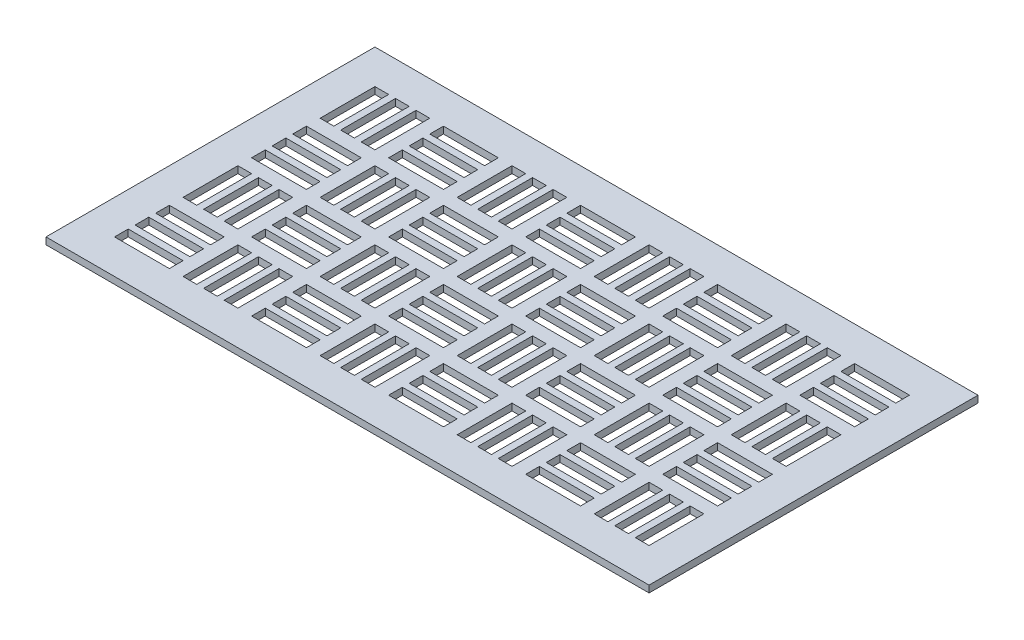
SolidWorks part; units mm, degrees
ref_plane "Front Plane" through (0, 0, 0) normal (0, 0, 1) x (1, 0, 0)
ref_plane "Top Plane" through (0, 0, 0) normal (0, 1, 0) x (1, 0, 0)
ref_plane "Right Plane" through (0, 0, 0) normal (1, 0, 0) x (0, 0, -1)
sketch "Sketch2" plane through (0, 0, 0) normal (0, 1, 0) x (1, 0, 0)
  line L0 (-284.5131, 55.5629) -> (-284.5131, 4.7629)
  line L1 (-328.9631, -217.4871) -> (229.8369, -217.4871)
  line L2 (-328.9631, -217.4871) -> (-328.9631, 87.3129)
  line L3 (-328.9631, 87.3129) -> (229.8369, 87.3129)
  line L4 (229.8369, -217.4871) -> (229.8369, 87.3129)
  line L5 (-316.2631, 74.6129) -> (217.1369, 74.6129)
  line L6 (-316.2631, 74.6129) -> (-316.2631, -204.7871)
  line L7 (-316.2631, -204.7871) -> (217.1369, -204.7871)
  line L8 (217.1369, 74.6129) -> (217.1369, -204.7871)
  line L9 (-297.2131, 55.5629) -> (-284.5131, 55.5629)
  line L10 (-297.2131, 55.5629) -> (-297.2131, 4.7629)
  line L11 (-297.2131, 4.7629) -> (-284.5131, 4.7629)
  line L12 (-246.4131, 55.5629) -> (-246.4131, 4.7629)
  line L13 (-233.7131, 55.5629) -> (-182.9131, 55.5629)
  line L14 (-233.7131, 55.5629) -> (-233.7131, 42.8629)
  line L15 (-233.7131, 4.7629) -> (-182.9131, 4.7629)
  line L16 (-182.9131, 55.5629) -> (-182.9131, 42.8629)
  line L17 (-233.7131, -7.9371) -> (-221.0131, -7.9371)
  line L18 (-233.7131, -7.9371) -> (-233.7131, -58.7371)
  line L19 (-233.7131, -58.7371) -> (-221.0131, -58.7371)
  line L20 (-182.9131, -7.9371) -> (-182.9131, -58.7371)
  line L21 (-246.4131, -7.9371) -> (-297.2131, -7.9371)
  line L22 (-246.4131, -7.9371) -> (-246.4131, -20.6371)
  line L23 (-246.4131, -58.7371) -> (-297.2131, -58.7371)
  line L24 (-297.2131, -7.9371) -> (-297.2131, -20.6371)
  line L25 (-259.1131, 4.7629) -> (-246.4131, 4.7629)
  line L26 (-278.1631, 4.7629) -> (-278.1631, 55.5629)
  line L27 (-278.1631, 55.5629) -> (-265.4631, 55.5629)
  line L28 (-265.4631, 55.5629) -> (-265.4631, 4.7629)
  line L29 (-278.1631, 55.5629) -> (-265.4631, 55.5629)
  line L30 (-259.1131, 4.7629) -> (-259.1131, 55.5629)
  line L31 (-221.0131, -7.9371) -> (-221.0131, -58.7371)
  line L32 (-233.7131, 17.4629) -> (-233.7131, 4.7629)
  line L33 (-214.6631, -58.7371) -> (-214.6631, -7.9371)
  line L34 (-214.6631, -7.9371) -> (-201.9631, -7.9371)
  line L35 (-201.9631, -7.9371) -> (-201.9631, -58.7371)
  line L36 (-182.9131, 17.4629) -> (-182.9131, 4.7629)
  line L37 (-195.6131, -58.7371) -> (-195.6131, -7.9371)
  line L38 (-233.7131, 42.8629) -> (-182.9131, 42.8629)
  line L39 (-278.1631, 4.7629) -> (-265.4631, 4.7629)
  line L40 (-182.9131, 36.5129) -> (-233.7131, 36.5129)
  line L41 (-233.7131, 36.5129) -> (-233.7131, 23.8129)
  line L42 (-233.7131, 23.8129) -> (-182.9131, 23.8129)
  line L43 (-259.1131, 55.5629) -> (-246.4131, 55.5629)
  line L44 (-182.9131, 17.4629) -> (-233.7131, 17.4629)
  line L45 (-297.2131, -20.6371) -> (-246.4131, -20.6371)
  line L46 (-246.4131, -46.0371) -> (-246.4131, -58.7371)
  line L47 (-246.4131, -26.9871) -> (-297.2131, -26.9871)
  line L48 (-297.2131, -26.9871) -> (-297.2131, -39.6871)
  line L49 (-297.2131, -39.6871) -> (-246.4131, -39.6871)
  line L50 (-195.6131, -58.7371) -> (-182.9131, -58.7371)
  line L51 (-246.4131, -46.0371) -> (-297.2131, -46.0371)
  line L52 (-297.2131, -46.0371) -> (-297.2131, -58.7371)
  line L53 (-297.2131, -26.9871) -> (-297.2131, -39.6871)
  line L54 (-246.4131, -26.9871) -> (-246.4131, -39.6871)
  line L55 (-214.6631, -7.9371) -> (-201.9631, -7.9371)
  line L56 (-195.6131, -7.9371) -> (-182.9131, -7.9371)
  line L57 (-214.6631, -58.7371) -> (-201.9631, -58.7371)
  line L58 (-233.7131, 36.5129) -> (-233.7131, 23.8129)
  line L59 (-182.9131, 36.5129) -> (-182.9131, 23.8129)
  line L60 (-170.2131, 55.5629) -> (-170.2131, 4.7629)
  line L61 (-157.5131, 55.5629) -> (-157.5131, 4.7629)
  line L62 (-170.2131, 55.5629) -> (-157.5131, 55.5629)
  line L63 (-170.2131, 4.7629) -> (-157.5131, 4.7629)
  line L64 (-151.1631, 4.7629) -> (-151.1631, 55.5629)
  line L65 (-138.4631, 55.5629) -> (-138.4631, 4.7629)
  line L66 (-132.1131, 4.7629) -> (-132.1131, 55.5629)
  line L67 (-119.4131, 55.5629) -> (-119.4131, 4.7629)
  line L68 (-132.1131, 55.5629) -> (-119.4131, 55.5629)
  line L69 (-151.1631, 55.5629) -> (-138.4631, 55.5629)
  line L70 (-151.1631, 4.7629) -> (-138.4631, 4.7629)
  line L71 (-132.1131, 4.7629) -> (-119.4131, 4.7629)
  line L72 (-106.7131, 4.7629) -> (-55.9131, 4.7629)
  line L73 (-55.9131, 17.4629) -> (-106.7131, 17.4629)
  line L74 (-106.7131, 23.8129) -> (-55.9131, 23.8129)
  line L75 (-55.9131, 36.5129) -> (-106.7131, 36.5129)
  line L76 (-106.7131, 42.8629) -> (-55.9131, 42.8629)
  line L77 (-106.7131, 55.5629) -> (-55.9131, 55.5629)
  line L78 (-55.9131, -7.9371) -> (-55.9131, -58.7371)
  line L79 (-68.6131, -58.7371) -> (-68.6131, -7.9371)
  line L80 (-74.9631, -7.9371) -> (-74.9631, -58.7371)
  line L81 (-87.6631, -58.7371) -> (-87.6631, -7.9371)
  line L82 (-94.0131, -7.9371) -> (-94.0131, -58.7371)
  line L83 (-106.7131, -7.9371) -> (-106.7131, -58.7371)
  line L84 (-119.4131, -58.7371) -> (-170.2131, -58.7371)
  line L85 (-119.4131, -46.0371) -> (-119.4131, -58.7371)
  line L86 (-119.4131, -46.0371) -> (-170.2131, -46.0371)
  line L87 (-170.2131, -39.6871) -> (-119.4131, -39.6871)
  line L88 (-119.4131, -26.9871) -> (-119.4131, -39.6871)
  line L89 (-119.4131, -26.9871) -> (-170.2131, -26.9871)
  line L90 (-170.2131, -20.6371) -> (-119.4131, -20.6371)
  line L91 (-119.4131, -7.9371) -> (-119.4131, -20.6371)
  line L92 (-119.4131, -7.9371) -> (-170.2131, -7.9371)
  line L93 (-170.2131, -7.9371) -> (-170.2131, -20.6371)
  line L94 (-170.2131, -26.9871) -> (-170.2131, -39.6871)
  line L95 (-170.2131, -46.0371) -> (-170.2131, -58.7371)
  line L96 (-106.7131, -58.7371) -> (-94.0131, -58.7371)
  line L97 (-87.6631, -58.7371) -> (-74.9631, -58.7371)
  line L98 (-68.6131, -58.7371) -> (-55.9131, -58.7371)
  line L99 (-68.6131, -7.9371) -> (-55.9131, -7.9371)
  line L100 (-55.9131, 17.4629) -> (-55.9131, 4.7629)
  line L101 (-55.9131, 36.5129) -> (-55.9131, 23.8129)
  line L102 (-55.9131, 55.5629) -> (-55.9131, 42.8629)
  line L103 (-106.7131, 55.5629) -> (-106.7131, 42.8629)
  line L104 (-106.7131, 36.5129) -> (-106.7131, 23.8129)
  line L105 (-106.7131, 17.4629) -> (-106.7131, 4.7629)
  line L106 (-106.7131, -7.9371) -> (-94.0131, -7.9371)
  line L107 (-87.6631, -7.9371) -> (-74.9631, -7.9371)
  line L108 (-43.2131, 55.5629) -> (-43.2131, 4.7629)
  line L109 (-30.5131, 55.5629) -> (-30.5131, 4.7629)
  line L110 (-43.2131, 55.5629) -> (-30.5131, 55.5629)
  line L111 (-43.2131, 4.7629) -> (-30.5131, 4.7629)
  line L112 (-24.1631, 4.7629) -> (-24.1631, 55.5629)
  line L113 (-11.4631, 55.5629) -> (-11.4631, 4.7629)
  line L114 (-5.1131, 4.7629) -> (-5.1131, 55.5629)
  line L115 (7.5869, 55.5629) -> (7.5869, 4.7629)
  line L116 (-5.1131, 55.5629) -> (7.5869, 55.5629)
  line L117 (-24.1631, 55.5629) -> (-11.4631, 55.5629)
  line L118 (-24.1631, 4.7629) -> (-11.4631, 4.7629)
  line L119 (-5.1131, 4.7629) -> (7.5869, 4.7629)
  line L120 (20.2869, 4.7629) -> (71.0869, 4.7629)
  line L121 (71.0869, 17.4629) -> (20.2869, 17.4629)
  line L122 (20.2869, 23.8129) -> (71.0869, 23.8129)
  line L123 (71.0869, 36.5129) -> (20.2869, 36.5129)
  line L124 (20.2869, 42.8629) -> (71.0869, 42.8629)
  line L125 (20.2869, 55.5629) -> (71.0869, 55.5629)
  line L126 (71.0869, -7.9371) -> (71.0869, -58.7371)
  line L127 (58.3869, -58.7371) -> (58.3869, -7.9371)
  line L128 (52.0369, -7.9371) -> (52.0369, -58.7371)
  line L129 (39.3369, -58.7371) -> (39.3369, -7.9371)
  line L130 (32.9869, -7.9371) -> (32.9869, -58.7371)
  line L131 (20.2869, -7.9371) -> (20.2869, -58.7371)
  line L132 (7.5869, -58.7371) -> (-43.2131, -58.7371)
  line L133 (7.5869, -46.0371) -> (7.5869, -58.7371)
  line L134 (7.5869, -46.0371) -> (-43.2131, -46.0371)
  line L135 (-43.2131, -39.6871) -> (7.5869, -39.6871)
  line L136 (7.5869, -26.9871) -> (7.5869, -39.6871)
  line L137 (7.5869, -26.9871) -> (-43.2131, -26.9871)
  line L138 (-43.2131, -20.6371) -> (7.5869, -20.6371)
  line L139 (7.5869, -7.9371) -> (7.5869, -20.6371)
  line L140 (7.5869, -7.9371) -> (-43.2131, -7.9371)
  line L141 (-43.2131, -7.9371) -> (-43.2131, -20.6371)
  line L142 (-43.2131, -26.9871) -> (-43.2131, -39.6871)
  line L143 (-43.2131, -46.0371) -> (-43.2131, -58.7371)
  line L144 (20.2869, -58.7371) -> (32.9869, -58.7371)
  line L145 (39.3369, -58.7371) -> (52.0369, -58.7371)
  line L146 (58.3869, -58.7371) -> (71.0869, -58.7371)
  line L147 (58.3869, -7.9371) -> (71.0869, -7.9371)
  line L148 (71.0869, 17.4629) -> (71.0869, 4.7629)
  line L149 (71.0869, 36.5129) -> (71.0869, 23.8129)
  line L150 (71.0869, 55.5629) -> (71.0869, 42.8629)
  line L151 (20.2869, 55.5629) -> (20.2869, 42.8629)
  line L152 (20.2869, 36.5129) -> (20.2869, 23.8129)
  line L153 (20.2869, 17.4629) -> (20.2869, 4.7629)
  line L154 (20.2869, -7.9371) -> (32.9869, -7.9371)
  line L155 (39.3369, -7.9371) -> (52.0369, -7.9371)
  line L156 (83.7869, 55.5629) -> (83.7869, 4.7629)
  line L157 (96.4869, 55.5629) -> (96.4869, 4.7629)
  line L158 (83.7869, 55.5629) -> (96.4869, 55.5629)
  line L159 (83.7869, 4.7629) -> (96.4869, 4.7629)
  line L160 (102.8369, 4.7629) -> (102.8369, 55.5629)
  line L161 (115.5369, 55.5629) -> (115.5369, 4.7629)
  line L162 (121.8869, 4.7629) -> (121.8869, 55.5629)
  line L163 (134.5869, 55.5629) -> (134.5869, 4.7629)
  line L164 (121.8869, 55.5629) -> (134.5869, 55.5629)
  line L165 (102.8369, 55.5629) -> (115.5369, 55.5629)
  line L166 (102.8369, 4.7629) -> (115.5369, 4.7629)
  line L167 (121.8869, 4.7629) -> (134.5869, 4.7629)
  line L168 (147.2869, 4.7629) -> (198.0869, 4.7629)
  line L169 (198.0869, 17.4629) -> (147.2869, 17.4629)
  line L170 (147.2869, 23.8129) -> (198.0869, 23.8129)
  line L171 (198.0869, 36.5129) -> (147.2869, 36.5129)
  line L172 (147.2869, 42.8629) -> (198.0869, 42.8629)
  line L173 (147.2869, 55.5629) -> (198.0869, 55.5629)
  line L174 (198.0869, -7.9371) -> (198.0869, -58.7371)
  line L175 (185.3869, -58.7371) -> (185.3869, -7.9371)
  line L176 (179.0369, -7.9371) -> (179.0369, -58.7371)
  line L177 (166.3369, -58.7371) -> (166.3369, -7.9371)
  line L178 (159.9869, -7.9371) -> (159.9869, -58.7371)
  line L179 (147.2869, -7.9371) -> (147.2869, -58.7371)
  line L180 (134.5869, -58.7371) -> (83.7869, -58.7371)
  line L181 (134.5869, -46.0371) -> (134.5869, -58.7371)
  line L182 (134.5869, -46.0371) -> (83.7869, -46.0371)
  line L183 (83.7869, -39.6871) -> (134.5869, -39.6871)
  line L184 (134.5869, -26.9871) -> (134.5869, -39.6871)
  line L185 (134.5869, -26.9871) -> (83.7869, -26.9871)
  line L186 (83.7869, -20.6371) -> (134.5869, -20.6371)
  line L187 (134.5869, -7.9371) -> (134.5869, -20.6371)
  line L188 (134.5869, -7.9371) -> (83.7869, -7.9371)
  line L189 (83.7869, -7.9371) -> (83.7869, -20.6371)
  line L190 (83.7869, -26.9871) -> (83.7869, -39.6871)
  line L191 (83.7869, -46.0371) -> (83.7869, -58.7371)
  line L192 (147.2869, -58.7371) -> (159.9869, -58.7371)
  line L193 (166.3369, -58.7371) -> (179.0369, -58.7371)
  line L194 (185.3869, -58.7371) -> (198.0869, -58.7371)
  line L195 (185.3869, -7.9371) -> (198.0869, -7.9371)
  line L196 (198.0869, 17.4629) -> (198.0869, 4.7629)
  line L197 (198.0869, 36.5129) -> (198.0869, 23.8129)
  line L198 (198.0869, 55.5629) -> (198.0869, 42.8629)
  line L199 (147.2869, 55.5629) -> (147.2869, 42.8629)
  line L200 (147.2869, 36.5129) -> (147.2869, 23.8129)
  line L201 (147.2869, 17.4629) -> (147.2869, 4.7629)
  line L202 (147.2869, -7.9371) -> (159.9869, -7.9371)
  line L203 (166.3369, -7.9371) -> (179.0369, -7.9371)
  line L204 (-170.2131, -71.4371) -> (-170.2131, -122.2371)
  line L205 (-157.5131, -71.4371) -> (-157.5131, -122.2371)
  line L206 (-170.2131, -71.4371) -> (-157.5131, -71.4371)
  line L207 (-170.2131, -122.2371) -> (-157.5131, -122.2371)
  line L208 (-151.1631, -122.2371) -> (-151.1631, -71.4371)
  line L209 (-138.4631, -71.4371) -> (-138.4631, -122.2371)
  line L210 (-132.1131, -122.2371) -> (-132.1131, -71.4371)
  line L211 (-119.4131, -71.4371) -> (-119.4131, -122.2371)
  line L212 (-132.1131, -71.4371) -> (-119.4131, -71.4371)
  line L213 (-151.1631, -71.4371) -> (-138.4631, -71.4371)
  line L214 (-151.1631, -122.2371) -> (-138.4631, -122.2371)
  line L215 (-132.1131, -122.2371) -> (-119.4131, -122.2371)
  line L216 (-106.7131, -122.2371) -> (-55.9131, -122.2371)
  line L217 (-55.9131, -109.5371) -> (-106.7131, -109.5371)
  line L218 (-106.7131, -103.1871) -> (-55.9131, -103.1871)
  line L219 (-55.9131, -90.4871) -> (-106.7131, -90.4871)
  line L220 (-106.7131, -84.1371) -> (-55.9131, -84.1371)
  line L221 (-106.7131, -71.4371) -> (-55.9131, -71.4371)
  line L222 (-55.9131, -134.9371) -> (-55.9131, -185.7371)
  line L223 (-68.6131, -185.7371) -> (-68.6131, -134.9371)
  line L224 (-74.9631, -134.9371) -> (-74.9631, -185.7371)
  line L225 (-87.6631, -185.7371) -> (-87.6631, -134.9371)
  line L226 (-94.0131, -134.9371) -> (-94.0131, -185.7371)
  line L227 (-106.7131, -134.9371) -> (-106.7131, -185.7371)
  line L228 (-119.4131, -185.7371) -> (-170.2131, -185.7371)
  line L229 (-119.4131, -173.0371) -> (-119.4131, -185.7371)
  line L230 (-119.4131, -173.0371) -> (-170.2131, -173.0371)
  line L231 (-170.2131, -166.6871) -> (-119.4131, -166.6871)
  line L232 (-119.4131, -153.9871) -> (-119.4131, -166.6871)
  line L233 (-119.4131, -153.9871) -> (-170.2131, -153.9871)
  line L234 (-170.2131, -147.6371) -> (-119.4131, -147.6371)
  line L235 (-119.4131, -134.9371) -> (-119.4131, -147.6371)
  line L236 (-119.4131, -134.9371) -> (-170.2131, -134.9371)
  line L237 (-170.2131, -134.9371) -> (-170.2131, -147.6371)
  line L238 (-170.2131, -153.9871) -> (-170.2131, -166.6871)
  line L239 (-170.2131, -173.0371) -> (-170.2131, -185.7371)
  line L240 (-106.7131, -185.7371) -> (-94.0131, -185.7371)
  line L241 (-87.6631, -185.7371) -> (-74.9631, -185.7371)
  line L242 (-68.6131, -185.7371) -> (-55.9131, -185.7371)
  line L243 (-68.6131, -134.9371) -> (-55.9131, -134.9371)
  line L244 (-55.9131, -109.5371) -> (-55.9131, -122.2371)
  line L245 (-55.9131, -90.4871) -> (-55.9131, -103.1871)
  line L246 (-55.9131, -71.4371) -> (-55.9131, -84.1371)
  line L247 (-106.7131, -71.4371) -> (-106.7131, -84.1371)
  line L248 (-106.7131, -90.4871) -> (-106.7131, -103.1871)
  line L249 (-106.7131, -109.5371) -> (-106.7131, -122.2371)
  line L250 (-106.7131, -134.9371) -> (-94.0131, -134.9371)
  line L251 (-87.6631, -134.9371) -> (-74.9631, -134.9371)
  line L252 (-43.2131, -71.4371) -> (-43.2131, -122.2371)
  line L253 (-30.5131, -71.4371) -> (-30.5131, -122.2371)
  line L254 (-43.2131, -71.4371) -> (-30.5131, -71.4371)
  line L255 (-43.2131, -122.2371) -> (-30.5131, -122.2371)
  line L256 (-24.1631, -122.2371) -> (-24.1631, -71.4371)
  line L257 (-11.4631, -71.4371) -> (-11.4631, -122.2371)
  line L258 (-5.1131, -122.2371) -> (-5.1131, -71.4371)
  line L259 (7.5869, -71.4371) -> (7.5869, -122.2371)
  line L260 (-5.1131, -71.4371) -> (7.5869, -71.4371)
  line L261 (-24.1631, -71.4371) -> (-11.4631, -71.4371)
  line L262 (-24.1631, -122.2371) -> (-11.4631, -122.2371)
  line L263 (-5.1131, -122.2371) -> (7.5869, -122.2371)
  line L264 (20.2869, -122.2371) -> (71.0869, -122.2371)
  line L265 (71.0869, -109.5371) -> (20.2869, -109.5371)
  line L266 (20.2869, -103.1871) -> (71.0869, -103.1871)
  line L267 (71.0869, -90.4871) -> (20.2869, -90.4871)
  line L268 (20.2869, -84.1371) -> (71.0869, -84.1371)
  line L269 (20.2869, -71.4371) -> (71.0869, -71.4371)
  line L270 (71.0869, -134.9371) -> (71.0869, -185.7371)
  line L271 (58.3869, -185.7371) -> (58.3869, -134.9371)
  line L272 (52.0369, -134.9371) -> (52.0369, -185.7371)
  line L273 (39.3369, -185.7371) -> (39.3369, -134.9371)
  line L274 (32.9869, -134.9371) -> (32.9869, -185.7371)
  line L275 (20.2869, -134.9371) -> (20.2869, -185.7371)
  line L276 (7.5869, -185.7371) -> (-43.2131, -185.7371)
  line L277 (7.5869, -173.0371) -> (7.5869, -185.7371)
  line L278 (7.5869, -173.0371) -> (-43.2131, -173.0371)
  line L279 (-43.2131, -166.6871) -> (7.5869, -166.6871)
  line L280 (7.5869, -153.9871) -> (7.5869, -166.6871)
  line L281 (7.5869, -153.9871) -> (-43.2131, -153.9871)
  line L282 (-43.2131, -147.6371) -> (7.5869, -147.6371)
  line L283 (7.5869, -134.9371) -> (7.5869, -147.6371)
  line L284 (7.5869, -134.9371) -> (-43.2131, -134.9371)
  line L285 (-43.2131, -134.9371) -> (-43.2131, -147.6371)
  line L286 (-43.2131, -153.9871) -> (-43.2131, -166.6871)
  line L287 (-43.2131, -173.0371) -> (-43.2131, -185.7371)
  line L288 (20.2869, -185.7371) -> (32.9869, -185.7371)
  line L289 (39.3369, -185.7371) -> (52.0369, -185.7371)
  line L290 (58.3869, -185.7371) -> (71.0869, -185.7371)
  line L291 (58.3869, -134.9371) -> (71.0869, -134.9371)
  line L292 (71.0869, -109.5371) -> (71.0869, -122.2371)
  line L293 (71.0869, -90.4871) -> (71.0869, -103.1871)
  line L294 (71.0869, -71.4371) -> (71.0869, -84.1371)
  line L295 (20.2869, -71.4371) -> (20.2869, -84.1371)
  line L296 (20.2869, -90.4871) -> (20.2869, -103.1871)
  line L297 (20.2869, -109.5371) -> (20.2869, -122.2371)
  line L298 (20.2869, -134.9371) -> (32.9869, -134.9371)
  line L299 (39.3369, -134.9371) -> (52.0369, -134.9371)
  line L300 (83.7869, -71.4371) -> (83.7869, -122.2371)
  line L301 (96.4869, -71.4371) -> (96.4869, -122.2371)
  line L302 (83.7869, -71.4371) -> (96.4869, -71.4371)
  line L303 (83.7869, -122.2371) -> (96.4869, -122.2371)
  line L304 (102.8369, -122.2371) -> (102.8369, -71.4371)
  line L305 (115.5369, -71.4371) -> (115.5369, -122.2371)
  line L306 (121.8869, -122.2371) -> (121.8869, -71.4371)
  line L307 (134.5869, -71.4371) -> (134.5869, -122.2371)
  line L308 (121.8869, -71.4371) -> (134.5869, -71.4371)
  line L309 (102.8369, -71.4371) -> (115.5369, -71.4371)
  line L310 (102.8369, -122.2371) -> (115.5369, -122.2371)
  line L311 (121.8869, -122.2371) -> (134.5869, -122.2371)
  line L312 (147.2869, -122.2371) -> (198.0869, -122.2371)
  line L313 (198.0869, -109.5371) -> (147.2869, -109.5371)
  line L314 (147.2869, -103.1871) -> (198.0869, -103.1871)
  line L315 (198.0869, -90.4871) -> (147.2869, -90.4871)
  line L316 (147.2869, -84.1371) -> (198.0869, -84.1371)
  line L317 (147.2869, -71.4371) -> (198.0869, -71.4371)
  line L318 (198.0869, -134.9371) -> (198.0869, -185.7371)
  line L319 (185.3869, -185.7371) -> (185.3869, -134.9371)
  line L320 (179.0369, -134.9371) -> (179.0369, -185.7371)
  line L321 (166.3369, -185.7371) -> (166.3369, -134.9371)
  line L322 (159.9869, -134.9371) -> (159.9869, -185.7371)
  line L323 (147.2869, -134.9371) -> (147.2869, -185.7371)
  line L324 (134.5869, -185.7371) -> (83.7869, -185.7371)
  line L325 (134.5869, -173.0371) -> (134.5869, -185.7371)
  line L326 (134.5869, -173.0371) -> (83.7869, -173.0371)
  line L327 (83.7869, -166.6871) -> (134.5869, -166.6871)
  line L328 (134.5869, -153.9871) -> (134.5869, -166.6871)
  line L329 (134.5869, -153.9871) -> (83.7869, -153.9871)
  line L330 (83.7869, -147.6371) -> (134.5869, -147.6371)
  line L331 (134.5869, -134.9371) -> (134.5869, -147.6371)
  line L332 (134.5869, -134.9371) -> (83.7869, -134.9371)
  line L333 (83.7869, -134.9371) -> (83.7869, -147.6371)
  line L334 (83.7869, -153.9871) -> (83.7869, -166.6871)
  line L335 (83.7869, -173.0371) -> (83.7869, -185.7371)
  line L336 (147.2869, -185.7371) -> (159.9869, -185.7371)
  line L337 (166.3369, -185.7371) -> (179.0369, -185.7371)
  line L338 (185.3869, -185.7371) -> (198.0869, -185.7371)
  line L339 (185.3869, -134.9371) -> (198.0869, -134.9371)
  line L340 (198.0869, -109.5371) -> (198.0869, -122.2371)
  line L341 (198.0869, -90.4871) -> (198.0869, -103.1871)
  line L342 (198.0869, -71.4371) -> (198.0869, -84.1371)
  line L343 (147.2869, -71.4371) -> (147.2869, -84.1371)
  line L344 (147.2869, -90.4871) -> (147.2869, -103.1871)
  line L345 (147.2869, -109.5371) -> (147.2869, -122.2371)
  line L346 (147.2869, -134.9371) -> (159.9869, -134.9371)
  line L347 (166.3369, -134.9371) -> (179.0369, -134.9371)
  line L348 (-297.2131, -71.4371) -> (-297.2131, -122.2371)
  line L349 (-284.5131, -71.4371) -> (-284.5131, -122.2371)
  line L350 (-297.2131, -71.4371) -> (-284.5131, -71.4371)
  line L351 (-297.2131, -122.2371) -> (-284.5131, -122.2371)
  line L352 (-278.1631, -122.2371) -> (-278.1631, -71.4371)
  line L353 (-265.4631, -71.4371) -> (-265.4631, -122.2371)
  line L354 (-259.1131, -122.2371) -> (-259.1131, -71.4371)
  line L355 (-246.4131, -71.4371) -> (-246.4131, -122.2371)
  line L356 (-259.1131, -71.4371) -> (-246.4131, -71.4371)
  line L357 (-278.1631, -71.4371) -> (-265.4631, -71.4371)
  line L358 (-278.1631, -122.2371) -> (-265.4631, -122.2371)
  line L359 (-259.1131, -122.2371) -> (-246.4131, -122.2371)
  line L360 (-233.7131, -122.2371) -> (-182.9131, -122.2371)
  line L361 (-182.9131, -109.5371) -> (-233.7131, -109.5371)
  line L362 (-233.7131, -103.1871) -> (-182.9131, -103.1871)
  line L363 (-182.9131, -90.4871) -> (-233.7131, -90.4871)
  line L364 (-233.7131, -84.1371) -> (-182.9131, -84.1371)
  line L365 (-233.7131, -71.4371) -> (-182.9131, -71.4371)
  line L366 (-182.9131, -134.9371) -> (-182.9131, -185.7371)
  line L367 (-195.6131, -185.7371) -> (-195.6131, -134.9371)
  line L368 (-201.9631, -134.9371) -> (-201.9631, -185.7371)
  line L369 (-214.6631, -185.7371) -> (-214.6631, -134.9371)
  line L370 (-221.0131, -134.9371) -> (-221.0131, -185.7371)
  line L371 (-233.7131, -134.9371) -> (-233.7131, -185.7371)
  line L372 (-246.4131, -185.7371) -> (-297.2131, -185.7371)
  line L373 (-246.4131, -173.0371) -> (-246.4131, -185.7371)
  line L374 (-246.4131, -173.0371) -> (-297.2131, -173.0371)
  line L375 (-297.2131, -166.6871) -> (-246.4131, -166.6871)
  line L376 (-246.4131, -153.9871) -> (-246.4131, -166.6871)
  line L377 (-246.4131, -153.9871) -> (-297.2131, -153.9871)
  line L378 (-297.2131, -147.6371) -> (-246.4131, -147.6371)
  line L379 (-246.4131, -134.9371) -> (-246.4131, -147.6371)
  line L380 (-246.4131, -134.9371) -> (-297.2131, -134.9371)
  line L381 (-297.2131, -134.9371) -> (-297.2131, -147.6371)
  line L382 (-297.2131, -153.9871) -> (-297.2131, -166.6871)
  line L383 (-297.2131, -173.0371) -> (-297.2131, -185.7371)
  line L384 (-233.7131, -185.7371) -> (-221.0131, -185.7371)
  line L385 (-214.6631, -185.7371) -> (-201.9631, -185.7371)
  line L386 (-195.6131, -185.7371) -> (-182.9131, -185.7371)
  line L387 (-195.6131, -134.9371) -> (-182.9131, -134.9371)
  line L388 (-182.9131, -109.5371) -> (-182.9131, -122.2371)
  line L389 (-182.9131, -90.4871) -> (-182.9131, -103.1871)
  line L390 (-182.9131, -71.4371) -> (-182.9131, -84.1371)
  line L391 (-233.7131, -71.4371) -> (-233.7131, -84.1371)
  line L392 (-233.7131, -90.4871) -> (-233.7131, -103.1871)
  line L393 (-233.7131, -109.5371) -> (-233.7131, -122.2371)
  line L394 (-233.7131, -134.9371) -> (-221.0131, -134.9371)
  line L395 (-214.6631, -134.9371) -> (-201.9631, -134.9371)
  point P56 (-265.4631, 30.1629)
  dimension "D1" = 558.8
  dimension "D2" = 304.8
  dimension "D3" = 12.7
  dimension "D4" = 12.7
  dimension "D5" = 12.7
  dimension "D6" = 12.7
  dimension "D7" = 50.8
  dimension "D8" = 50.8
  dimension "D9" = 19.05
  dimension "D10" = 19.05
  dimension "D11" = 12.7
  dimension "D12" = 12.7
  dimension "D13" = 12.7
  dimension "D14" = 12.7
  dimension "D15" = 50.8
  dimension "D16" = 50.8
  dimension "D17" = 50.8
  dimension "D18" = 50.8
  dimension "D19" = 50.8
  dimension "D20" = 50.8
  dimension "D21" = 19.05
  dimension "D22" = 19.05
  dimension "D23" = 12.7
  dimension "D24" = 6.35
  dimension "D25" = 12.7
  dimension "D26" = 6.35
  dimension "D27" = 12.7
  dimension "D28" = 6.35
  dimension "D29" = 12.7
  dimension "D30" = 6.35
  dimension "D31" = 12.7
  dimension "D32" = 6.35
  dimension "D33" = 12.7
  dimension "D34" = 6.35
  dimension "D35" = 12.7
  dimension "D36" = 6.35
  dimension "D37" = 12.7
  dimension "D38" = 6.35
  dimension "D39" = 4
  dimension "D40" = 2
extrude "Boss-Extrude1" add sketch "Sketch2" along normal blind 6.35 contours L8 L5 L6 L7 L393 L361 L388 L360 L392 L363 L389 L362 L391 L365 L390 L364 L383 L374 L373 L372 L382 L377 L376 L375 L381 L380 L379 L378 L359 L354 L356 L355 L358 L352 L357 L353 L351 L348 L350 L349 L345 | L1 L4 L3 L2 L5 L8 L7 L6
